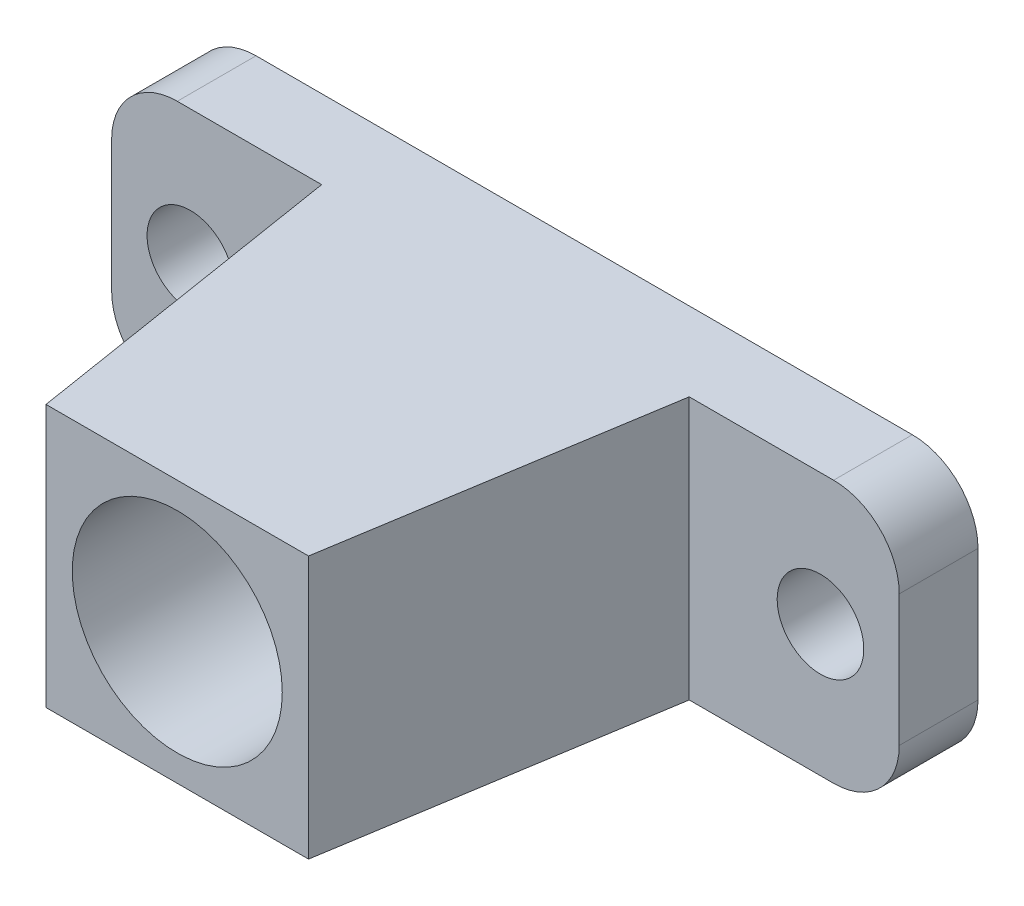
SolidWorks part; units mm, degrees
material "1.0503 (C45)"
ref_plane "前视基准面" through (0, 0, 0) normal (0, 0, 1) x (1, 0, 0)
ref_plane "上视基准面" through (0, 0, 0) normal (0, 1, 0) x (1, 0, 0)
ref_plane "右视基准面" through (0, 0, 0) normal (1, 0, 0) x (0, 0, -1)
sketch "草图1" plane through (0, 0, 0) normal (0, 0, 1) x (1, 0, 0)
  line L0 (0, 0) -> (0, 23.9578) construction
  line L1 (25, 10) -> (-25, 10)
  line L2 (30, 5) -> (30, -5)
  line L3 (25, -10) -> (-25, -10)
  line L4 (-30, 5) -> (-30, -5)
  line L5 (30, 10) -> (-30, -10) construction
  line L6 (30, -10) -> (-30, 10) construction
  circle A0 centre (-24, 0) radius 3.3
  circle A1 centre (24, 0) radius 3.3
  arc A2 (25, 10) -> (30, 5) centre (25, 5) cw
  arc A3 (30, -5) -> (25, -10) centre (25, -5) cw
  arc A4 (-25, -10) -> (-30, -5) centre (-25, -5) cw
  arc A5 (-25, 10) -> (-30, 5) centre (-25, 5) ccw
  point P0 (0, 0)
  dimension "D3" = 6.6
  dimension "D4" = 48
  dimension "D5" = 5
  dimension "D1" = 60
  dimension "D2" = 20
extrude "凸台-拉伸1" add sketch "草图1" along normal blind 6
sketch "草图2" plane through (0, 10, 0) normal (0, 1, 0) x (1, 0, 0)
  line L0 (14, -6) -> (-14, -6)
  line L1 (25, -6) -> (-25, -6) construction
  line L2 (-14, -6) -> (-10, -31)
  line L3 (-10, -31) -> (10, -31)
  line L4 (0, -31) -> (0, -6) construction
  line L5 (14, -6) -> (10, -31)
  dimension "D1" = 20
  dimension "D2" = 4
  dimension "D3" = 25
extrude "凸台-拉伸3" add sketch "草图2" against normal up to surface (20 mm away) up to face at (0, -10, 3)
sketch "草图3" plane through (0, 0, 31) normal (0, 0, 1) x (1, 0, 0)
  circle A0 centre (0, 0) radius 8
extrude "切除-拉伸1" cut sketch "草图3" against normal through all
equation "\"6。6\"=6"
